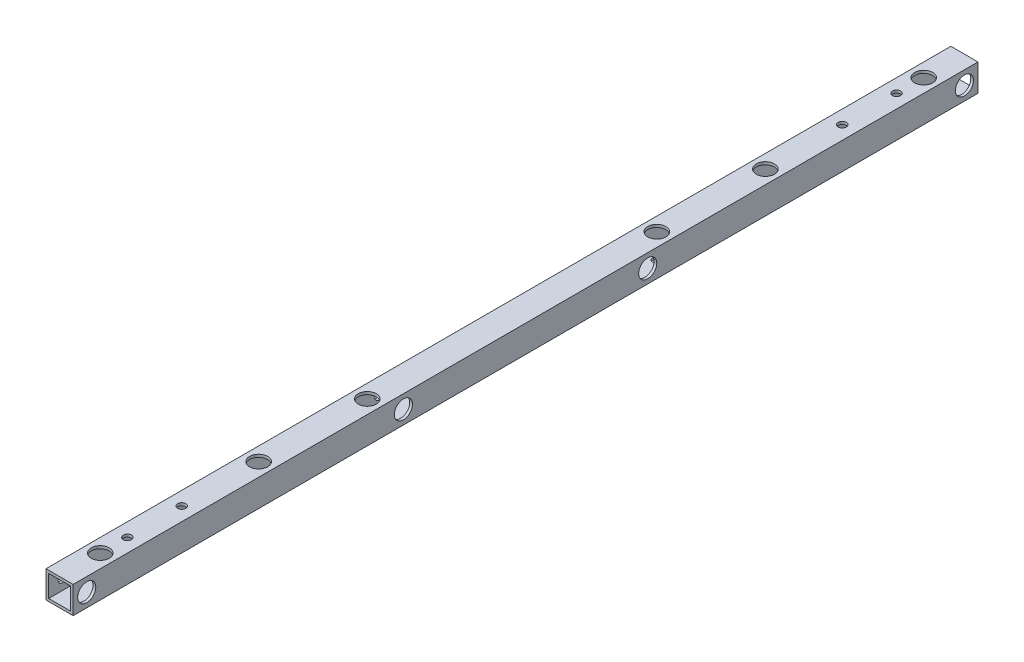
SolidWorks part; units mm, degrees
material "6063-T5"
ref_plane "正面" through (0, 0, 0) normal (0, 0, 1) x (1, 0, 0)
ref_plane "平面" through (0, 0, 0) normal (0, 1, 0) x (1, 0, 0)
ref_plane "右側面" through (0, 0, 0) normal (1, 0, 0) x (0, 0, -1)
sketch "ｽｹｯﾁ1" plane through (0, 0, 0) normal (0, 0, 1) x (1, 0, 0)
  line L1 (-7.5, -7.5) -> (7.5, -7.5)
  line L2 (-7.5, -7.5) -> (-7.5, 7.5)
  line L3 (-7.5, 7.5) -> (7.5, 7.5)
  line L4 (7.5, -7.5) -> (7.5, 7.5)
  line L5 (-7.5, -7.5) -> (7.5, 7.5) construction
  line L6 (-7.5, 7.5) -> (7.5, -7.5) construction
  line L7 (-6, -6) -> (6, -6)
  line L8 (-6, -6) -> (-6, 6)
  line L9 (-6, 6) -> (6, 6)
  line L10 (6, -6) -> (6, 6)
  line L11 (-6, -6) -> (6, 6) construction
  line L12 (-6, 6) -> (6, -6) construction
  point P0 (0, 0)
  point P6 (0, 0)
  dimension "D1" = 1.5
  dimension "D2" = 15
  dimension "D3" = 15
extrude "ﾎﾞｽ - 押し出し1" add sketch "ｽｹｯﾁ1" along normal blind 500
sketch "ｽｹｯﾁ2" plane through (7.5, 0, 0) normal (1, 0, 0) x (0, 0, -1)
  line L0 (-500, -7.5) -> (0, -7.5) construction
  line L1 (0, -7.5) -> (0, 7.5) construction
  line L2 (-500, -7.5) -> (-500, 7.5) construction
  line L3 (-500, 0) -> (0, 0) construction
  circle A4 centre (-492.5, 0) radius 2.25
  circle A8 centre (-7.5, 0) radius 2.25
  circle A9 centre (-317.5, 0) radius 2.25
  circle A10 centre (-182.5, 0) radius 2.25
  point P17 (-250, 0)
  dimension "D1" = 4.5
  dimension "D2" = 7.5
  dimension "D3" = 7.5
  dimension "D6" = 67.5
  dimension "D7" = 2
  dimension "D8" = 135
  dimension "D4" = 7.5
  dimension "D9" = 2
  dimension "D5" = 2
extrude "ｶｯﾄ - 押し出し1" cut sketch "ｽｹｯﾁ2" against normal blind 25
sketch "ｽｹｯﾁ3" plane through (0, 7.5, 0) normal (0, 1, 0) x (1, 0, 0)
  line L2 (7.5, -500) -> (7.5, 0) construction
  line L3 (7.5, 0) -> (-7.5, 0) construction
  circle A1 centre (0, -22.5) radius 2.25
  circle A6 centre (0, -477.5) radius 2.25
  circle A7 centre (0, -37.5) radius 2.25
  circle A9 centre (0, -462.5) radius 2.25
  circle A10 centre (0, -67.5) radius 2.25
  circle A11 centre (0, -432.5) radius 2.25
  dimension "D2" = 22.5
  dimension "D3" = 4.5
  dimension "D7" = 15
  dimension "D8" = 2
  dimension "D9" = 7.5
  dimension "D11" = 22.5
  dimension "D4" = 7.5
  dimension "D5" = 4.5
  dimension "D10" = 15
  dimension "D13" = 30
  dimension "D15" = 30
  dimension "D6" = 2
  dimension "D12" = 2
  dimension "D14" = 2
extrude "ｶｯﾄ - 押し出し2" cut sketch "ｽｹｯﾁ3" against normal blind 25
sketch "ｽｹｯﾁ4" plane through (0, -7.5, 0) normal (0, -1, 0) x (-1, 0, 0)
  line L0 (7.5, -500) -> (7.5, 0) construction
  line L1 (7.5, -500) -> (-7.5, -500) construction
  line L2 (7.5, 0) -> (-7.5, 0) construction
  circle A0 centre (0, -390) radius 2.25
  circle A1 centre (0, -330) radius 2.25
  circle A2 centre (0, -110) radius 2.25
  circle A3 centre (0, -170) radius 2.25
  dimension "D1" = 4.5
  dimension "D2" = 7.5
  dimension "D3" = 110
  dimension "D6" = 60
  dimension "D8" = 110
  dimension "D4" = 2
  dimension "D7" = 2
extrude "ｶｯﾄ - 押し出し3" cut sketch "ｽｹｯﾁ4" against normal blind 20
sketch "ｽｹｯﾁ5" plane through (0, 7.5, 0) normal (0, 1, 0) x (1, 0, 0)
  circle A0 centre (0, -22.5) radius 5
  circle A1 centre (0, -477.5) radius 5
  circle A2 centre (0, -390) radius 5
  circle A3 centre (0, -330) radius 5
  circle A4 centre (0, -110) radius 5
  circle A5 centre (0, -170) radius 5
  dimension "D1" = 10
  dimension "D2" = 10
  dimension "D3" = 10
  dimension "D4" = 10
  dimension "D5" = 10
  dimension "D6" = 10
extrude "ｶｯﾄ - 押し出し4" cut sketch "ｽｹｯﾁ5" against normal blind 10
sketch "ｽｹｯﾁ6" plane through (7.5, 0, 0) normal (1, 0, 0) x (0, 0, -1)
  circle A0 centre (-492.5, 0) radius 5
  circle A1 centre (-317.5, 0) radius 5
  circle A2 centre (-182.5, 0) radius 5
  circle A3 centre (-7.5, 0) radius 5
  dimension "D1" = 10
  dimension "D2" = 10
  dimension "D3" = 10
  dimension "D4" = 10
extrude "ｶｯﾄ - 押し出し5" cut sketch "ｽｹｯﾁ6" against normal blind 10
